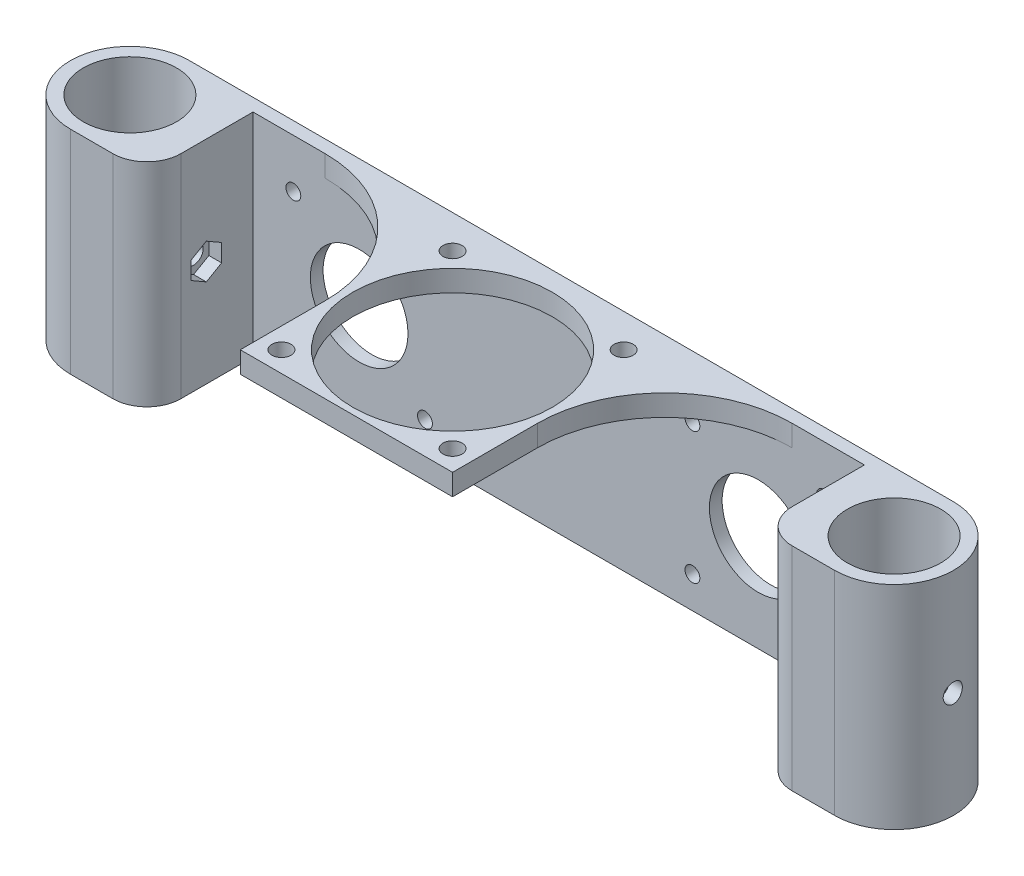
SolidWorks part; units mm, degrees
ref_plane "Front Plane" through (0, 0, 0) normal (0, 0, 1) x (1, 0, 0)
ref_plane "Top Plane" through (0, 0, 0) normal (0, 1, 0) x (1, 0, 0)
ref_plane "Right Plane" through (0, 0, 0) normal (1, 0, 0) x (0, 0, -1)
sketch "Sketch1" plane through (0, 0, 0) normal (0, 1, 0) x (1, 0, 0)
  line L0 (137.4606, -14.5) -> (119.4606, -14.5)
  line L1 (119.4606, -14.5) -> (119.4606, 10.5)
  line L2 (-42.5394, -14.5) -> (-24.5394, -14.5)
  line L3 (-42.5394, 13.5) -> (137.4606, 13.5)
  line L4 (119.4606, 10.5) -> (-24.5394, 10.5)
  line L5 (-24.5394, -14.5) -> (-24.5394, 10.5)
  circle A0 centre (-42.5394, -0.5) radius 11
  circle A1 centre (137.4606, -0.5) radius 11
  arc A2 (-42.5394, -14.5) -> (-42.5394, 13.5) centre (-42.5394, -0.5) cw
  arc A6 (137.4606, 13.5) -> (137.4606, -14.5) centre (137.4606, -0.5) cw
  dimension "D3" = 22
  dimension "D4" = 22
  dimension "D5" = 180
  dimension "D6" = 3
  dimension "D1" = 18
  dimension "D2" = 18
  dimension "D8" = 3
extrude "Boss-Extrude1" add sketch "Sketch1" along normal blind 50
fillet "Fillet1" radius 8 2 edges at (119.4606, 25, 14.5) (-24.5394, 25, 14.5)
sketch "Sketch2" plane through (0, 0, -10.5) normal (0, 0, 1) x (1, 0, 0)
  line L0 (47.4606, 0) -> (47.4606, 50) construction
  line L1 (-24.5394, 0) -> (119.4606, 0) construction
  line L2 (-24.5394, 50) -> (119.4606, 50) construction
  line L3 (0.4606, 23) -> (0.4606, 7.5) construction
  line L4 (0.4606, 7.5) -> (15.9606, 7.5) construction
  line L5 (0.4606, 23) -> (47.4606, 23) construction
  line L6 (0.4606, 7.5) -> (-15.0394, 7.5) construction
  line L7 (-15.0394, 7.5) -> (-15.0394, 38.5) construction
  line L8 (-15.0394, 38.5) -> (15.9606, 38.5) construction
  line L9 (15.9606, 38.5) -> (15.9606, 7.5) construction
  circle A0 centre (0.4606, 23) radius 11.5
  circle A1 centre (15.9606, 7.5) radius 1.75
  circle A2 centre (-15.0394, 7.5) radius 1.75
  circle A3 centre (-15.0394, 38.5) radius 1.75
  circle A4 centre (15.9606, 38.5) radius 1.75
  circle A5 centre (78.9606, 38.5) radius 1.75
  circle A6 centre (109.9606, 38.5) radius 1.75
  circle A7 centre (109.9606, 7.5) radius 1.75
  circle A8 centre (94.4606, 23) radius 11.5
  circle A9 centre (78.9606, 7.5) radius 1.75
  point P12 (-1.7517, 25)
  point P21 (0.4606, 23)
  point P30 (0, 0)
  dimension "D2" = 23
  dimension "D3" = 3.5
  dimension "D5" = 47
  dimension "D1" = 15.5
  dimension "D6" = 23
  dimension "D4" = 4
extrude "Cut-Extrude1" cut sketch "Sketch2" against normal blind 10
sketch "Sketch3" plane through (0, 0, -10.5) normal (0, 0, 1) x (1, 0, 0)
  line L0 (-24.5394, 50) -> (119.4606, 50) construction
  line L1 (72.4606, 50) -> (22.4606, 50)
  line L2 (72.4606, 50) -> (72.4606, 45)
  line L3 (72.4606, 45) -> (22.4606, 45)
  line L4 (22.4606, 50) -> (22.4606, 45)
  line L5 (-24.5394, 0) -> (119.4606, 0) construction
  point P8 (47.4606, 0)
  dimension "D1" = 50
  dimension "D2" = 25
  dimension "D3" = 5
extrude "Boss-Extrude2" add sketch "Sketch3" along normal blind 50
sketch "Sketch4" plane through (0, 45, 0) normal (0, -1, 0) x (-1, 0, 0)
  line L0 (-72.4606, 10.5) -> (-22.4606, -39.5) construction
  circle A0 centre (-47.4606, -14.5) radius 23.5
  circle A1 centre (-67.6131, 5.6525) radius 2.25
  circle A2 centre (-27.308, 5.6525) radius 2.25
  circle A3 centre (-27.308, -34.6525) radius 2.25
  circle A4 centre (-67.6131, -34.6525) radius 2.25
  point P17 (-47.4606, -14.5)
  dimension "D1" = 47
  dimension "D3" = 4.5
  dimension "D2" = 28.5
  dimension "D4" = 4
extrude "Cut-Extrude2" cut sketch "Sketch4" against normal blind 50
fillet "Fillet2" radius 30 2 edges at (72.4606, 47.5, -10.5) (22.4606, 47.5, -10.5)
ref_plane "Plane1" through (139.4606, 0, 0) normal (-1, 0, 0) x (0, 0, 1)
sketch "Sketch6" plane through (139.4606, 0, 0) normal (-1, 0, 0) x (0, 0, 1)
  line L0 (-10.3167, 0) -> (-10.3167, 50)
  line L1 (11.3167, 50) -> (11.3167, 0)
  line L2 (11.3167, 50) -> (11.3167, 0)
  line L3 (-10.3167, 0) -> (-10.3167, 50)
  circle A0 centre (0.5, 25) radius 2.25
  dimension "D1" = 4.5
extrude "Cut-Extrude3" cut sketch "Sketch6" against normal through all both and the other way through all contours A0
sketch "Sketch7" plane through (-24.5394, 0, 0) normal (1, 0, 0) x (0, 0, -1)
  line L1 (-0.5, 20.8431) -> (3.1, 22.9215)
  line L2 (3.1, 22.9215) -> (3.1, 27.0785)
  line L3 (3.1, 27.0785) -> (-0.5, 29.1569)
  line L4 (-0.5, 29.1569) -> (-4.1, 27.0785)
  line L5 (-4.1, 27.0785) -> (-4.1, 22.9215)
  line L6 (-4.1, 22.9215) -> (-0.5, 20.8431)
  circle A0 centre (-0.5, 25) radius 3.6 construction
  dimension "D1" = 7.2
extrude "Cut-Extrude4" cut sketch "Sketch7" against normal blind 3
ref_plane "Plane2" through (47.4606, 0, 0) normal (-1, 0, 0) x (0, 0, 1)
mirror "Mirror1" about plane through (47.4606, 0, 0) normal (-1, 0, 0) of "Cut-Extrude4"
